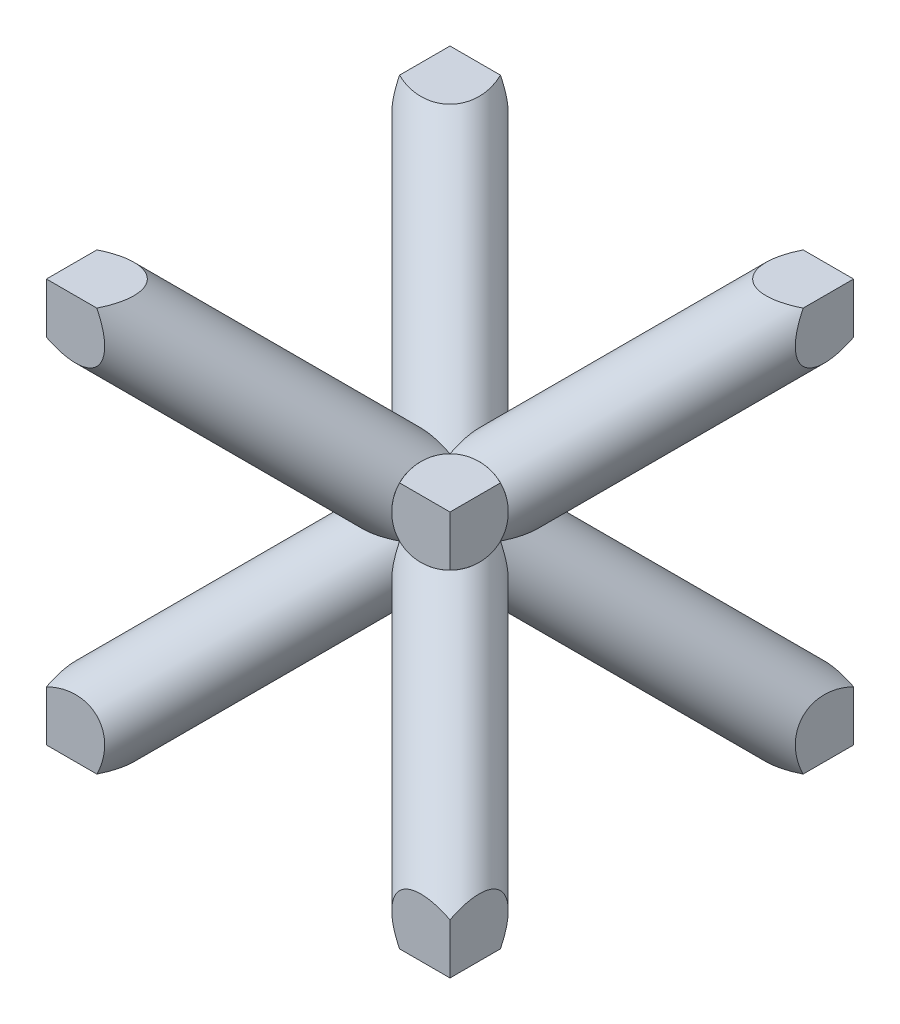
SolidWorks part; units mm, degrees
ref_plane "Front Plane" through (0, 0, 0) normal (0, 0, 1) x (1, 0, 0)
ref_plane "Top Plane" through (0, 0, 0) normal (0, 1, 0) x (1, 0, 0)
ref_plane "Right Plane" through (0, 0, 0) normal (1, 0, 0) x (0, 0, -1)
sketch "Sketch1" plane through (0, 0, 0) normal (0, 1, 0) x (1, 0, 0)
  line L1 (-5, -5) -> (5, -5)
  line L2 (-5, -5) -> (-5, 5)
  line L3 (-5, 5) -> (5, 5)
  line L4 (5, -5) -> (5, 5)
  line L5 (-5, -5) -> (5, 5) construction
  line L6 (-5, 5) -> (5, -5) construction
  point P0 (0, 0)
  dimension "D1" = 10
extrude "Frame" add sketch "Sketch1" along normal blind 10
shell "Shell2" thickness 1
sketch3d "3DSketch1"
  line L0 (5, 9, 4) -> (5, 9, -4)
  line L1 (5, 9, 4) -> (5, 1, 4)
  line L2 (5, 1, 4) -> (5, 1, -4)
  line L3 (5, 9, -4) -> (5, 1, -4)
  line L4 (5, 9, 4) -> (5, 9, -4)
  line L5 (5, 9, 4) -> (5, 1, 4)
  line L6 (5, 1, 4) -> (5, 1, -4)
  line L7 (5, 9, -4) -> (5, 1, -4)
  dimension "D1" = 1
extrude "Cut-Extrude1" cut sketch "3DSketch1" along direction (1, 0, 0) on the side against the normal through all
sketch3d "3DSketch2"
  line L0 (-4, 9, 5) -> (-4, 1, 5)
  line L1 (-4, 1, 5) -> (4, 1, 5)
  line L2 (4, 9, 5) -> (4, 1, 5)
  line L3 (-4, 9, 5) -> (4, 9, 5)
  line L4 (-4, 9, 5) -> (-4, 1, 5)
  line L5 (-4, 1, 5) -> (4, 1, 5)
  line L6 (4, 9, 5) -> (4, 1, 5)
  line L7 (-4, 9, 5) -> (4, 9, 5)
  dimension "D1" = 1
extrude "Cut-Extrude2" cut sketch "3DSketch2" along direction (0, 0, 1) on the side of the normal through all
ref_plane "Plane1" through (-6, 6, 6) normal (-0.5774, 0.5774, 0.5774) x (0.8165, 0.4082, 0.4082)
sketch "Sketch5" plane through (-6, 6, 6) normal (-0.5774, 0.5774, 0.5774) x (0.8165, 0.4082, 0.4082)
  circle A1 centre (2.0412, 3.5355) radius 0.8165
extrude "Boss-Extrude6" add sketch "Sketch5" against normal blind 15.05
ref_plane "Plane2" through (-2.6667, -2.6667, -2.6667) normal (0.5774, 0.5774, 0.5774) x (0.8165, -0.4082, -0.4082)
sketch "Sketch9" plane through (-2.6667, -2.6667, -2.6667) normal (0.5774, 0.5774, 0.5774) x (0.8165, -0.4082, -0.4082)
  circle A0 centre (-2.0412, 3.5355) radius 0.8165
extrude "Boss-Extrude5" add sketch "Sketch9" along normal blind 15
ref_plane "Plane3" through (2.6667, -2.6667, 2.6667) normal (-0.5774, 0.5774, -0.5774) x (-0.8165, -0.4082, 0.4082)
sketch "Sketch10" plane through (2.6667, -2.6667, 2.6667) normal (-0.5774, 0.5774, -0.5774) x (-0.8165, -0.4082, 0.4082)
  circle A0 centre (-2.0412, 3.5355) radius 0.8165
extrude "Boss-Extrude7" add sketch "Sketch10" along normal blind 15
ref_plane "Plane4" through (6, 6, -6) normal (0.5774, 0.5774, -0.5774) x (-0.8165, 0.4082, -0.4082)
sketch "Sketch11" plane through (6, 6, -6) normal (0.5774, 0.5774, -0.5774) x (-0.8165, 0.4082, -0.4082)
  circle A0 centre (2.0412, 3.5355) radius 0.8165
extrude "Boss-Extrude8" add sketch "Sketch11" against normal blind 15
sketch "Sketch15" plane through (5, 0, 0) normal (1, 0, 0) x (0, 0, -1)
  line L0 (-4, 10) -> (-4, 9)
  line L1 (-4, 9) -> (4, 9)
  line L2 (4, 9) -> (4, 10)
  line L3 (4, 10) -> (-4, 10)
  line L10 (-4, 1) -> (-4, 0)
  line L11 (-4, 0) -> (4, 0)
  line L14 (-4, 1) -> (4, 1)
  line L15 (4, 1) -> (4, 0)
  line L16 (-5, 0) -> (5, 0) construction
extrude "Cut-Extrude8" cut sketch "Sketch15" against normal through all
sketch "Sketch16" plane through (0, 0, 5) normal (0, 0, 1) x (1, 0, 0)
  line L0 (-5, 10) -> (5, 10)
  line L1 (5, 10) -> (5, 9)
  line L2 (5, 9) -> (-5, 9)
  line L3 (-5, 9) -> (-5, 10)
  line L4 (-5, 1) -> (-5, 0)
  line L5 (-5, 0) -> (5, 0)
  line L6 (5, 0) -> (5, 1)
  line L7 (5, 1) -> (-5, 1)
  line L8 (4, 1) -> (-4, 1) construction
  line L9 (-4, 9) -> (4, 9) construction
extrude "Cut-Extrude10" cut sketch "Sketch16" against normal through all
sketch "Sketch17" plane through (0, 0, 5) normal (0, 0, 1) x (1, 0, 0)
  line L0 (-5, 9) -> (-4, 9)
  line L1 (-4, 9) -> (-4, 1)
  line L2 (-4, 1) -> (-5, 1)
  line L3 (-5, 1) -> (-5, 9)
  line L4 (4, 9) -> (5, 9)
  line L5 (5, 9) -> (5, 1)
  line L6 (5, 1) -> (4, 1)
  line L7 (4, 1) -> (4, 9)
  line L8 (4, 9) -> (5, 9) construction
  point P3 (-4, 9)
extrude "Cut-Extrude12" cut sketch "Sketch17" against normal through all
ref_plane "Plane5" through (0, 0, 5) normal (0, 0, 1) x (1, 0, 0)
sketch "Sketch18" plane through (0, 0, 5) normal (0, 0, 1) x (1, 0, 0)
  line L0 (-4, 9) -> (-2.8453, 9)
  line L2 (-2.8453, 9) -> (-2.8453, 1)
  line L3 (-2.8453, 1) -> (-4, 1)
  line L4 (-4, 1) -> (-4, 9)
  line L5 (0, 0) -> (0, 11.5072) construction
  line L6 (2.8453, 1) -> (4, 1)
  line L7 (4, 1) -> (4, 9)
  line L8 (4, 9) -> (2.8453, 9)
  line L9 (2.8453, 9) -> (2.8453, 1)
  line L10 (-2.8453, 9) -> (-4, 9) construction
  point P3 (-4, 9)
extrude "Cut-Extrude13" cut sketch "Sketch18" against normal blind 1
ref_plane "Plane7" through (-0.004, 0.004, -5.004) normal (-0.0008, 0.0008, -1) x (-1, 0, 0.0008)
ref_plane "Plane9" through (0, 0, -5) normal (0, 0, -1) x (-1, 0, 0)
sketch "Sketch19" plane through (0, 0, -5) normal (0, 0, -1) x (-1, 0, 0)
  line L0 (-4, 1) -> (-2.8453, 1)
  line L1 (-2.8453, 1) -> (-2.8453, 9)
  line L2 (-2.8453, 9) -> (-4, 9)
  line L3 (-4, 9) -> (-4, 1)
  line L4 (0, 5) -> (0, 0) construction
  line L5 (4, 1) -> (2.8453, 1)
  line L6 (2.8453, 9) -> (4, 9)
  line L7 (4, 9) -> (4, 1)
  line L8 (2.8453, 1) -> (2.8453, 9)
extrude "Cut-Extrude14" cut sketch "Sketch19" against normal blind 1
delete or keep bodies "Body-Delete/Keep 1" type delete bodies bodies 175 173
equation "\"L\"= 15.00"
equation "\"D1@Boss-Extrude6\"= \"L\""
equation "\"D1@Boss-Extrude5\"=\"L\""
equation "\"D1@Boss-Extrude7\"=\"L\""
equation "\"D1@Boss-Extrude8\"=\"L\""
